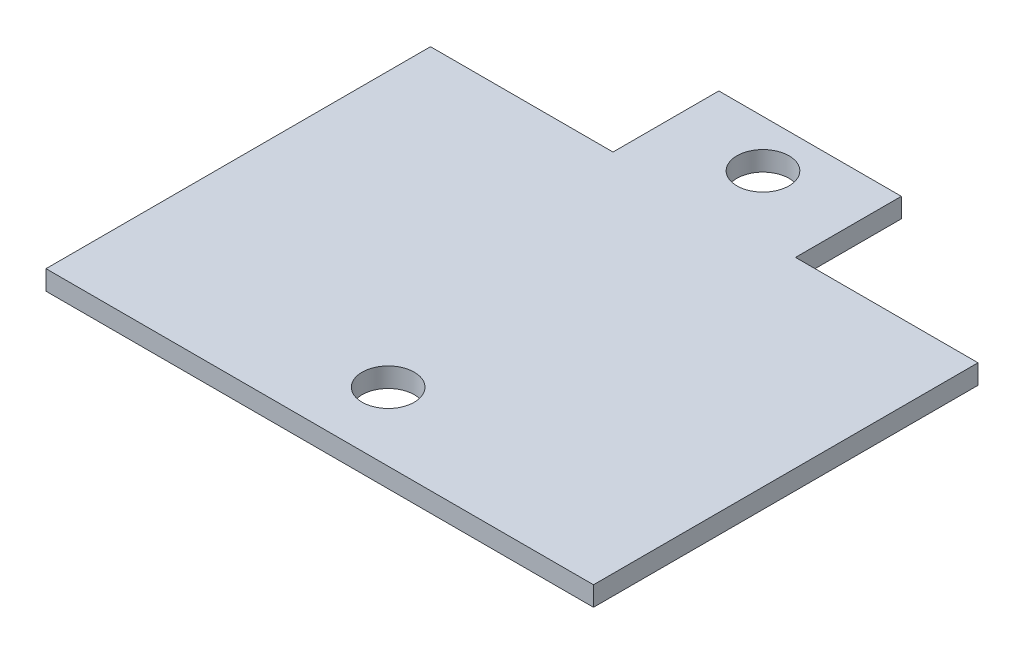
SolidWorks part; units mm, degrees
ref_plane "Спереди" through (0, 0, 0) normal (0, 0, 1) x (1, 0, 0)
ref_plane "Сверху" through (0, 0, 0) normal (0, 1, 0) x (1, 0, 0)
ref_plane "Справа" through (0, 0, 0) normal (1, 0, 0) x (0, 0, -1)
sketch "Эскиз1" plane through (0, 0, 0) normal (0, 1, 0) x (1, 0, 0)
  line L0 (0, 29.4965) -> (14, 29.4965)
  line L1 (0, 0) -> (42, 0)
  line L2 (0, 0) -> (0, 29.4965)
  line L4 (42, 0) -> (42, 29.4965)
  line L5 (14, 29.4965) -> (14, 37.6149)
  line L6 (14, 37.6149) -> (28, 37.6149)
  line L7 (28, 37.6149) -> (28, 29.4965)
  line L8 (28, 29.4965) -> (42, 29.4965)
  line L9 (21, 0) -> (21, 75.2298) construction
  circle A1 centre (21, 5.25) radius 2
  circle A2 centre (21, 34) radius 2
  point P13 (21, 37.6149)
  point P14 (0, 0)
extrude "Бобышка-Вытянуть1" add sketch "Эскиз1" along normal blind 1.5
